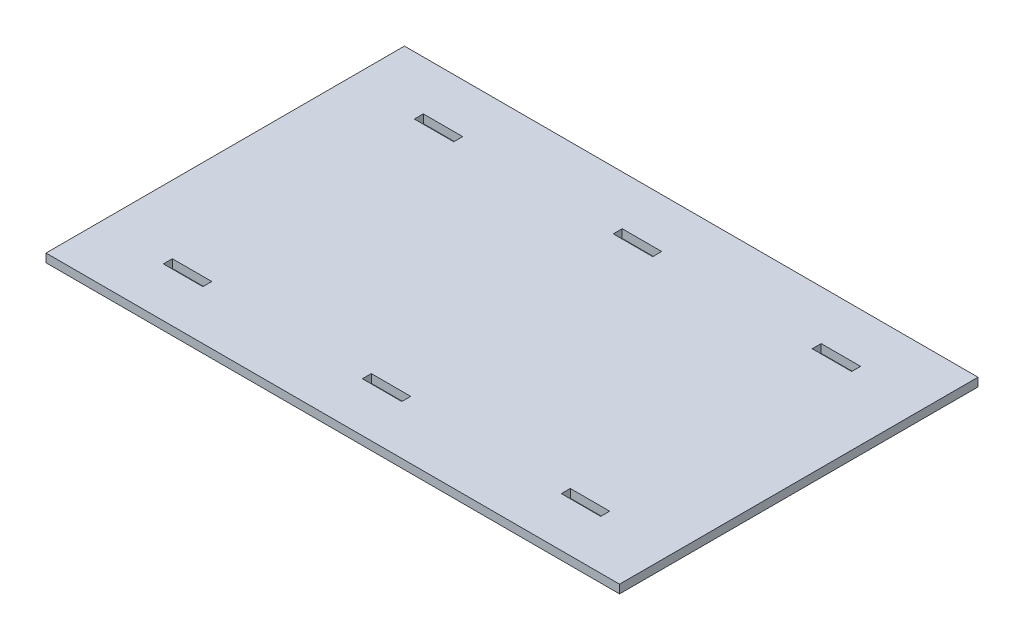
SolidWorks part; units mm, degrees
ref_plane "Front Plane" through (0, 0, 0) normal (0, 0, 1) x (1, 0, 0)
ref_plane "Top Plane" through (0, 0, 0) normal (0, 1, 0) x (1, 0, 0)
ref_plane "Right Plane" through (0, 0, 0) normal (1, 0, 0) x (0, 0, -1)
sketch "Sketch1" plane through (0, 0, 0) normal (0, 1, 0) x (1, 0, 0)
  line L1 (-101.6, -63.5) -> (101.6, -63.5)
  line L2 (-101.6, -63.5) -> (-101.6, 63.5)
  line L3 (-101.6, 63.5) -> (101.6, 63.5)
  line L4 (101.6, -63.5) -> (101.6, 63.5)
  line L5 (-101.6, -63.5) -> (101.6, 63.5) construction
  line L6 (-101.6, 63.5) -> (101.6, -63.5) construction
  point P0 (0, 0)
  dimension "D1" = 203.2
  dimension "D2" = 127
extrude "Extrude1" add sketch "Sketch1" along normal blind 2.9972
sketch "Sketch2" plane through (0, 2.9972, 0) normal (0, 1, 0) x (-1, 0, 0)
  line L0 (0, -63.5) -> (0, 0) construction
  line L1 (-101.6, -63.5) -> (101.6, -63.5) construction
  line L2 (0, 0) -> (101.6, 0) construction
  line L3 (101.6, -63.5) -> (101.6, 63.5) construction
  line L4 (-63.5, -46.0375) -> (-63.5, -42.8625)
  line L5 (77.47, -46.0375) -> (63.5, -46.0375)
  line L6 (77.47, -46.0375) -> (77.47, -42.8625)
  line L7 (77.47, -42.8625) -> (63.5, -42.8625)
  line L8 (63.5, -46.0375) -> (63.5, -42.8625)
  line L9 (6.985, -46.0375) -> (-6.985, -46.0375)
  line L10 (6.985, -46.0375) -> (6.985, -42.8625)
  line L11 (6.985, -42.8625) -> (-6.985, -42.8625)
  line L12 (-6.985, -46.0375) -> (-6.985, -42.8625)
  line L13 (6.985, -46.0375) -> (-6.985, -42.8625) construction
  line L14 (6.985, -42.8625) -> (-6.985, -46.0375) construction
  line L15 (-77.47, -42.8625) -> (-63.5, -42.8625)
  line L16 (-77.47, -46.0375) -> (-77.47, -42.8625)
  line L17 (-77.47, -46.0375) -> (-63.5, -46.0375)
  line L18 (6.985, 42.8625) -> (-6.985, 46.0375) construction
  line L19 (6.985, 46.0375) -> (-6.985, 42.8625) construction
  line L20 (-77.47, 46.0375) -> (-63.5, 46.0375)
  line L21 (-77.47, 46.0375) -> (-77.47, 42.8625)
  line L22 (-77.47, 42.8625) -> (-63.5, 42.8625)
  line L23 (-6.985, 46.0375) -> (-6.985, 42.8625)
  line L24 (6.985, 42.8625) -> (-6.985, 42.8625)
  line L25 (6.985, 46.0375) -> (6.985, 42.8625)
  line L26 (6.985, 46.0375) -> (-6.985, 46.0375)
  line L27 (63.5, 46.0375) -> (63.5, 42.8625)
  line L28 (77.47, 42.8625) -> (63.5, 42.8625)
  line L29 (77.47, 46.0375) -> (77.47, 42.8625)
  line L30 (77.47, 46.0375) -> (63.5, 46.0375)
  line L31 (-63.5, 46.0375) -> (-63.5, 42.8625)
  point P12 (0, -44.45)
  point P33 (0, 44.45)
  dimension "D1" = 13.97
  dimension "D2" = 3.175
  dimension "D3" = 88.9
  dimension "D4" = 63.5
extrude "Slots" cut sketch "Sketch2" against normal through all
